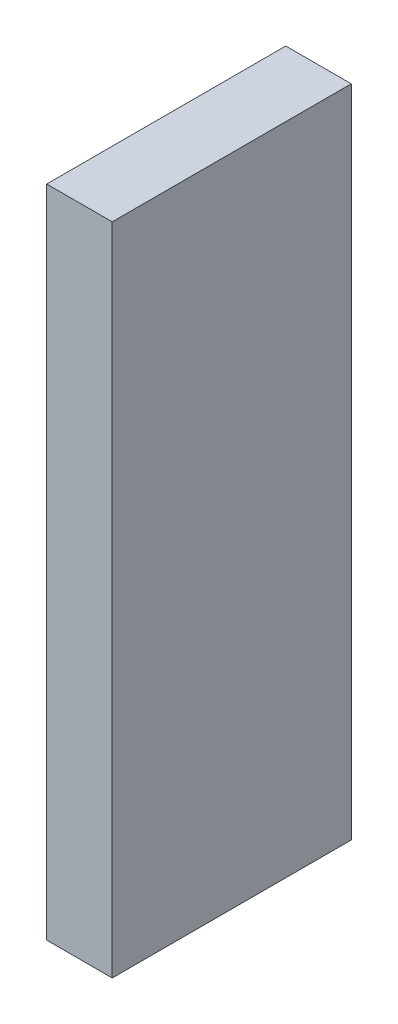
SolidWorks part; units mm, degrees
ref_plane "Front Plane" through (0, 0, 0) normal (0, 0, 1) x (1, 0, 0)
ref_plane "Top Plane" through (0, 0, 0) normal (0, 1, 0) x (1, 0, 0)
ref_plane "Right Plane" through (0, 0, 0) normal (1, 0, 0) x (0, 0, -1)
sketch "Sketch2" plane through (0, 0, 0) normal (0, 0, 1) x (1, 0, 0)
  line L1 (-1.27, 12.7) -> (1.27, 12.7)
  line L2 (-1.27, 12.7) -> (-1.27, -12.7)
  line L3 (-1.27, -12.7) -> (1.27, -12.7)
  line L4 (1.27, 12.7) -> (1.27, -12.7)
  line L5 (-1.27, 12.7) -> (1.27, -12.7) construction
  line L6 (-1.27, -12.7) -> (1.27, 12.7) construction
  point P0 (0, 0)
  dimension "D1" = 2.54
  dimension "D2" = 25.4
extrude "Boss-Extrude1" add sketch "Sketch2" along normal mid plane 9.271
